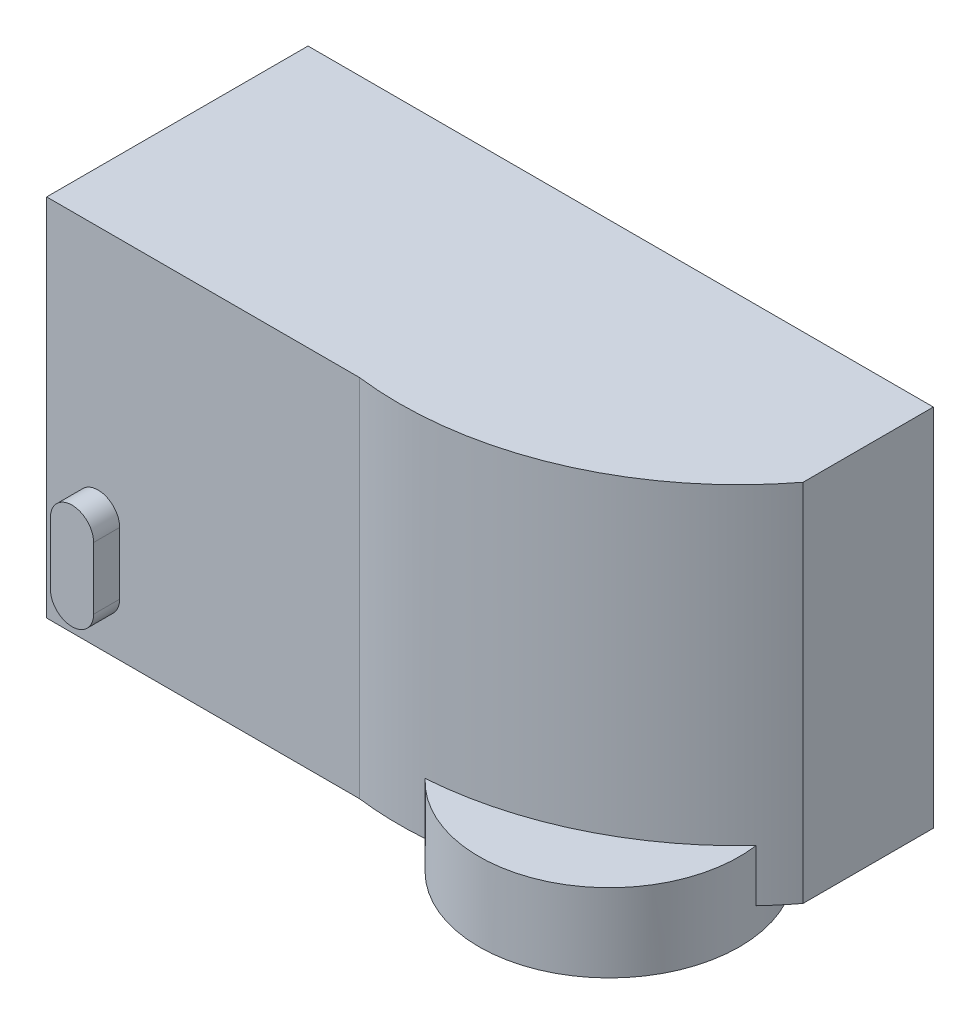
SolidWorks part; units mm, degrees
ref_plane "Front Plane" through (0, 0, 0) normal (0, 0, 1) x (1, 0, 0)
ref_plane "Top Plane" through (0, 0, 0) normal (0, 1, 0) x (1, 0, 0)
ref_plane "Right Plane" through (0, 0, 0) normal (1, 0, 0) x (0, 0, -1)
sketch "Sketch4" plane through (0, 0, 0) normal (0, 0, 1) x (1, 0, 0)
  line L1 (-60, 35) -> (60, 35)
  line L2 (-60, 35) -> (-60, -35)
  line L3 (-60, -35) -> (60, -35)
  line L4 (60, 35) -> (60, -35)
  line L5 (-60, 35) -> (60, -35) construction
  line L6 (-60, -35) -> (60, 35) construction
  point P0 (0, 0)
extrude "Boss-Extrude1" add sketch "Sketch4" against normal blind 10
sketch "Sketch5" plane through (0, 0, 0) normal (0, 0, 1) x (1, 0, 0)
  circle A0 centre (0, 0) radius 5
extrude "Cut-Extrude1" cut sketch "Sketch5" against normal blind 40
sketch "Sketch8" plane through (0, -35, 0) normal (0, -1, 0) x (1, 0, 0)
  line L0 (-60, -10) -> (-60, 40.1548)
  line L1 (-60, 40.1548) -> (0, 40.1548)
  line L2 (60, 15) -> (60, -10)
  line L7 (60, 0) -> (-60, 0)
  line L8 (-60, 0) -> (-60, -10)
  line L9 (-60, -10) -> (60, -10)
  line L10 (60, -10) -> (60, 0)
  line L13 (-60, -10) -> (60, -10)
  arc A0 (0, 40.1548) -> (60, 15) centre (8.1589, -24.5189) cw
  point P4 (0, 40.1548)
  dimension "D1" = 0
extrude "Boss-Extrude2" add sketch "Sketch8" against normal blind 70
sketch "Sketch9" plane through (0, 0, -10) normal (0, 0, -1) x (-1, 0, 0)
  circle A0 centre (0, 0) radius 5
extrude "Cut-Extrude2" cut sketch "Sketch9" against normal blind 15
sketch "Sketch11" plane through (0, -35, 0) normal (0, -1, 0) x (1, 0, 0)
  circle A1 centre (31.1174, 23.3063) radius 25
extrude "Boss-Extrude3" add sketch "Sketch11" along normal blind 5 and the other way blind 10
sketch "Sketch12" plane through (0, -40, 0) normal (0, -1, 0) x (1, 0, 0)
  circle A0 centre (31.1174, 23.3063) radius 5
extrude "Cut-Extrude3" cut sketch "Sketch12" against normal blind 7
sketch "Sketch14" plane through (0, 0, 40.1548) normal (0, 0, 1) x (1, 0, 0)
  line L0 (-50.1337, -12.9283) -> (-50.1337, -24.8464) construction
  line L1 (-45.9883, -12.9283) -> (-45.9883, -24.8464)
  line L2 (-54.2791, -12.9283) -> (-54.2791, -24.8464)
  arc A0 (-45.9883, -12.9283) -> (-54.2791, -12.9283) centre (-50.1337, -12.9283) ccw
  arc A1 (-54.2791, -24.8464) -> (-45.9883, -24.8464) centre (-50.1337, -24.8464) ccw
  point P2 (-50.1337, -18.8874)
extrude "Boss-Extrude5" add sketch "Sketch14" along normal blind 5
sketch "Sketch15" plane through (-60, 0, 0) normal (-1, 0, 0) x (0, 0, 1)
  line L1 (-2.9496, 28.1938) -> (1.5504, 28.1938)
  line L2 (-2.9496, 28.1938) -> (-2.9496, 18.1938)
  line L3 (-2.9496, 18.1938) -> (1.5504, 18.1938)
  line L4 (1.5504, 28.1938) -> (1.5504, 18.1938)
  line L5 (-2.9496, 28.1938) -> (1.5504, 18.1938) construction
  line L6 (-2.9496, 18.1938) -> (1.5504, 28.1938) construction
  line L7 (4.2746, 28.1938) -> (4.2746, 18.1938)
  line L8 (8.7746, 18.1938) -> (4.2746, 28.1938) construction
  line L9 (8.7746, 28.1938) -> (4.2746, 18.1938) construction
  line L10 (8.7746, 18.1938) -> (4.2746, 18.1938)
  line L11 (8.7746, 28.1938) -> (8.7746, 18.1938)
  line L12 (8.7746, 28.1938) -> (4.2746, 28.1938)
  point P0 (-0.6996, 23.1938)
  point P11 (6.5246, 23.1938)
extrude "Cut-Extrude4" cut sketch "Sketch15" against normal blind 8
sketch "Sketch16" plane through (-52, 0, 0) normal (-1, 0, 0) x (0, 0, 1)
  line L5 (-2.4201, 27.7882) -> (-0.8511, 27.7882)
  line L6 (-2.4201, 27.7882) -> (-2.4201, 19.0873)
  line L7 (-2.4201, 19.0873) -> (-0.8511, 19.0873)
  line L8 (-0.8511, 27.7882) -> (-0.8511, 19.0873)
  line L9 (-2.4201, 27.7882) -> (-0.8511, 19.0873) construction
  line L10 (-2.4201, 19.0873) -> (-0.8511, 27.7882) construction
  line L11 (4.9971, 27.7882) -> (6.4234, 27.7882)
  line L12 (4.9971, 27.7882) -> (4.9971, 19.0873)
  line L13 (4.9971, 19.0873) -> (6.4234, 19.0873)
  line L14 (6.4234, 27.7882) -> (6.4234, 19.0873)
  line L15 (4.9971, 27.7882) -> (6.4234, 19.0873) construction
  line L16 (4.9971, 19.0873) -> (6.4234, 27.7882) construction
  point P0 (-1.6356, 23.4377)
  point P5 (5.7103, 23.4377)
extrude "Boss-Extrude6" add sketch "Sketch16" along normal blind 8
sketch "Sketch17" plane through (-60, 0, 0) normal (-1, 0, 0) x (0, 0, 1)
  line L1 (-4.2657, -28.8582) -> (36.4345, -28.8582)
  line L2 (-4.2657, -28.8582) -> (-4.2657, -0.5942)
  line L3 (-4.2657, -0.5942) -> (36.4345, -0.5942)
  line L4 (36.4345, -28.8582) -> (36.4345, -0.5942)
extrude "Boss-Extrude7" add sketch "Sketch17" along normal blind 1
sketch "Sketch18" plane through (-61, 0, 0) normal (-1, 0, 0) x (0, 0, 1)
  line L5 (-0.5069, -8.2642) -> (2.3797, -8.2898)
  line L6 (2.3797, -8.2898) -> (3.8452, -5.8027)
  line L7 (3.8452, -5.8027) -> (2.4241, -3.29)
  line L8 (2.4241, -3.29) -> (-0.4625, -3.2644)
  line L9 (-0.4625, -3.2644) -> (-1.928, -5.7515)
  line L10 (-1.928, -5.7515) -> (-0.5069, -8.2642)
  line L12 (34.0968, -5.7515) -> (32.6757, -8.2642)
  line L13 (32.6313, -3.2644) -> (34.0968, -5.7515)
  line L15 (29.7447, -3.29) -> (32.6313, -3.2644)
  line L16 (28.3236, -5.8027) -> (29.7447, -3.29)
  line L17 (29.7891, -8.2898) -> (28.3236, -5.8027)
  line L18 (32.6757, -8.2642) -> (29.7891, -8.2898)
  line L19 (-1.928, -23.701) -> (-0.5069, -21.1882)
  line L20 (-0.4625, -26.188) -> (-1.928, -23.701)
  line L21 (2.4241, -26.1624) -> (-0.4625, -26.188)
  line L22 (3.8452, -23.6497) -> (2.4241, -26.1624)
  line L23 (2.3797, -21.1626) -> (3.8452, -23.6497)
  line L24 (-0.5069, -21.1882) -> (2.3797, -21.1626)
  line L25 (32.6757, -21.1882) -> (29.7891, -21.1626)
  line L26 (29.7891, -21.1626) -> (28.3236, -23.6497)
  line L27 (28.3236, -23.6497) -> (29.7447, -26.1624)
  line L28 (29.7447, -26.1624) -> (32.6313, -26.188)
  line L29 (32.6313, -26.188) -> (34.0968, -23.701)
  line L30 (34.0968, -23.701) -> (32.6757, -21.1882)
  circle A0 centre (0.9586, -5.7771) radius 2.5 construction
extrude "Boss-Extrude8" add sketch "Sketch18" along normal blind 1.5
